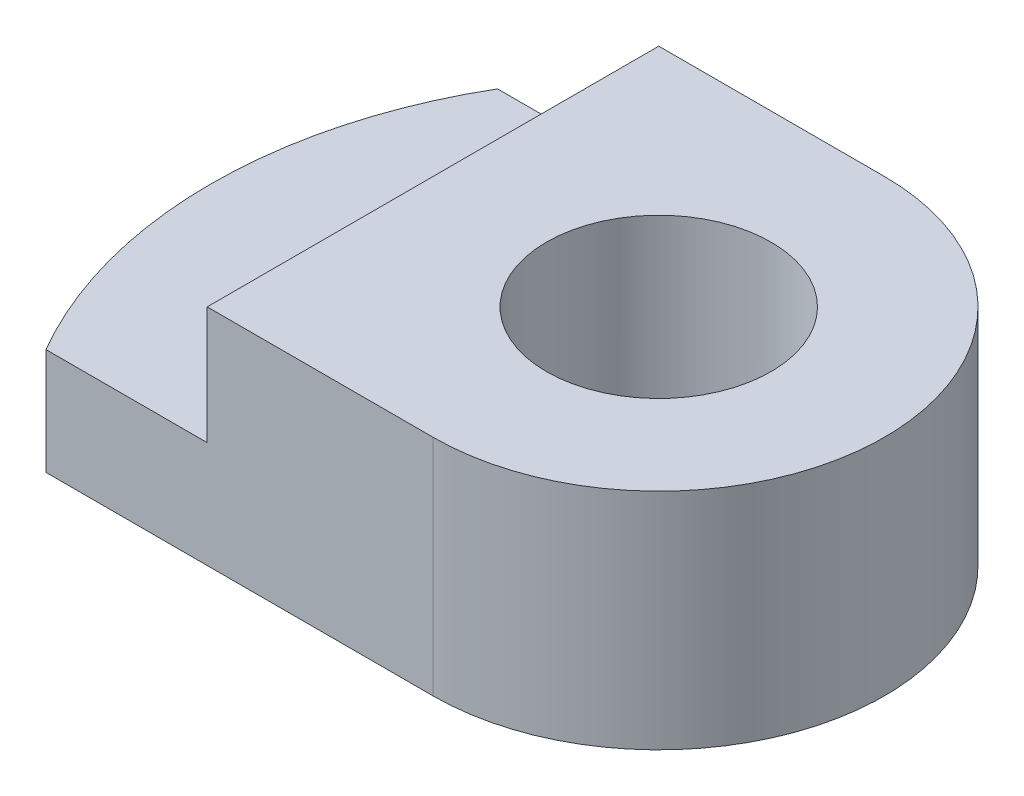
SolidWorks part; units mm, degrees
material "Gray Cast Iron"
ref_plane "Front Plane" through (0, 0, 0) normal (0, 0, 1) x (1, 0, 0)
ref_plane "Top Plane" through (0, 0, 0) normal (0, 1, 0) x (1, 0, 0)
ref_plane "Right Plane" through (0, 0, 0) normal (1, 0, 0) x (0, 0, -1)
sketch "Sketch1" plane through (0, 0, 0) normal (0, 1, 0) x (1, 0, 0)
  circle A0 centre (0, 0) radius 38.1
  circle A1 centre (0, 0) radius 9.5467
  dimension "D1" = 76.2
extrude "Boss-Extrude1" add sketch "Sketch1" along normal blind 38.1
ref_plane "Plane1" through (0, 0, 38.1) normal (0, 0, 1) x (1, 0, 0)
sketch "Sketch2" plane through (0, 0, 38.1) normal (0, 0, 1) x (1, 0, 0)
  line L0 (38.1, 19.05) -> (0, 19.05)
  line L1 (38.1, 0) -> (38.1, 38.1) construction
  line L2 (0, 19.05) -> (0, 0)
  line L3 (0, 0) -> (38.1, 0)
  line L4 (38.1, 0) -> (38.1, 19.05)
extrude "Cut-Extrude1" cut sketch "Sketch2" against normal blind 144.78
sketch "Sketch3" plane through (0, 19.05, 0) normal (0, -1, 0) x (1, 0, 0)
  line L0 (0, -19.2) -> (-32.9085, -19.2)
  line L1 (0, 19.2) -> (-32.9085, 19.2)
  arc A0 (0, -19.2) -> (0, 19.2) centre (0, 0) ccw
  circle A1 centre (0, 0) radius 38.1 construction
  arc A2 (-32.9085, -19.2) -> (-32.9085, 19.2) centre (0, 0) ccw
extrude "Cut-Extrude2" cut sketch "Sketch3" along direction (0, 1, 0) on the side against the normal blind 20.32 and the other way blind 22.86
sketch "Sketch4" plane through (0, 0, 19.2) normal (0, 0, 1) x (1, 0, 0)
  line L1 (0, 19.05) -> (-32.9085, 19.05)
  line L2 (0, 19.05) -> (0, 0)
  line L3 (0, 0) -> (-32.9085, 0)
  line L4 (-32.9085, 19.05) -> (-32.9085, 0)
sketch "Sketch5" plane through (0, 0, 19.2) normal (0, 0, 1) x (1, 0, 0)
  line L2 (0, 19.05) -> (-40.3427, 19.05)
  line L3 (0, 19.05) -> (0, -4.0596)
  line L4 (0, -4.0596) -> (-40.3427, -4.0596)
  line L5 (-40.3427, 19.05) -> (-40.3427, -4.0596)
extrude "Cut-Extrude4" cut sketch "Sketch5" against normal blind 53.594
sketch "Sketch6" plane through (0, 38.1, 0) normal (0, 1, 0) x (1, 0, 0)
  line L0 (-19.2, 19.2) -> (-19.2, -19.2)
  line L1 (0, 19.2) -> (-32.9085, 19.2) construction
  line L2 (-32.9085, -19.2) -> (0, -19.2) construction
  line L3 (-19.2, -19.2) -> (-32.9085, -19.2)
  line L4 (-19.2, 19.2) -> (-32.9085, 19.2)
  arc A1 (-32.9085, 19.2) -> (-32.9085, -19.2) centre (0, 0) ccw
extrude "Cut-Extrude5" cut sketch "Sketch6" against normal blind 10
